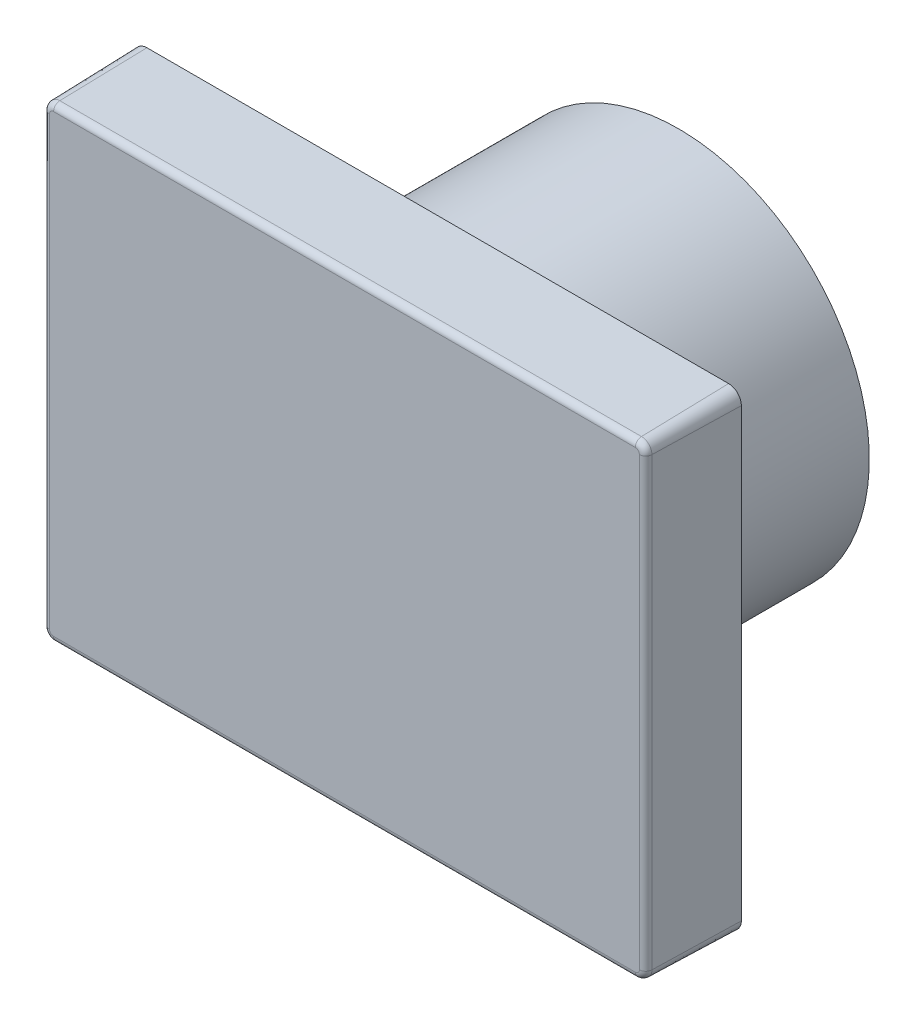
SolidWorks part; units mm, degrees
ref_plane "Front Plane" through (0, 0, 0) normal (0, 0, 1) x (1, 0, 0)
ref_plane "Top Plane" through (0, 0, 0) normal (0, 1, 0) x (1, 0, 0)
ref_plane "Right Plane" through (0, 0, 0) normal (1, 0, 0) x (0, 0, -1)
sketch "Sketch1" plane through (0, 0, 0) normal (0, 0, 1) x (1, 0, 0)
  line L1 (-30.25, -23.5) -> (30.25, -23.5)
  line L2 (-30.25, -23.5) -> (-30.25, 23.5)
  line L3 (-30.25, 23.5) -> (30.25, 23.5)
  line L4 (30.25, -23.5) -> (30.25, 23.5)
  line L5 (-30.25, -23.5) -> (30.25, 23.5) construction
  line L6 (-30.25, 23.5) -> (30.25, -23.5) construction
  point P0 (0, 0)
  dimension "D1" = 60.5
  dimension "D2" = 47
extrude "Boss-Extrude1" add sketch "Sketch1" along normal blind 9.3
fillet "Fillet1" radius 1.27 4 edges at (-30.25, -23.5, 4.65) (30.25, -23.5, 4.65) (30.25, 23.5, 4.65) (-30.25, 23.5, 4.65)
draft "Draft1" type of draft neutral plane draft angle 1.5 faces to draft 8 face at (-29.7465, -22.9965, 4.65) face at (0, -23.5, 4.65) face at (29.7465, -22.9965, 4.65) face at (30.25, 0, 4.65) face at (29.7465, 22.9965, 4.65) face at (0, 23.5, 4.65) face at (-30.25, 0, 4.65) face at (-29.7465, 22.9965, 4.65) neutral plane through (0, 0, 0) neutral plane normal (0, 0, -1) reverse direction yes parameters "D1"=1.5
fillet "Fillet2" radius 0.635 8 edges at (29.7058, -22.9558, 9.3) (0, -23.2565, 9.3) (-29.7058, -22.9558, 9.3) (-30.0065, 0, 9.3) (-29.7058, 22.9558, 9.3) (0, 23.2565, 9.3) (29.7058, 22.9558, 9.3) (30.0065, 0, 9.3)
sketch "Sketch3" plane through (0, 0, 0) normal (0, 0, -1) x (-1, 0, 0)
  circle A0 centre (0, 0) radius 19
  dimension "D1" = 38
extrude "Boss-Extrude2" add sketch "Sketch3" along normal blind 24
sketch "Sketch4" plane through (0, 0, -24) normal (0, 0, -1) x (-1, 0, 0)
  circle A0 centre (0, 0) radius 2
  dimension "D1" = 4
extrude "Boss-Extrude3" add sketch "Sketch4" along normal blind 4
